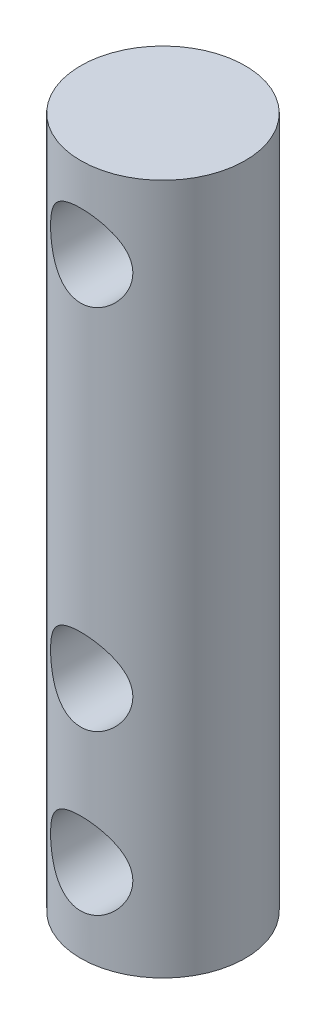
SolidWorks part; units mm, degrees
material "Plain Carbon Steel"
ref_plane "Front Plane" through (0, 0, 0) normal (0, 0, 1) x (1, 0, 0)
ref_plane "Top Plane" through (0, 0, 0) normal (0, 1, 0) x (1, 0, 0)
ref_plane "Right Plane" through (0, 0, 0) normal (1, 0, 0) x (0, 0, -1)
sketch "Sketch1" plane through (0, 0, 0) normal (0, 1, 0) x (1, 0, 0)
  circle A0 centre (0, 0) radius 2.5
  dimension "D1" = 5
extrude "Boss-Extrude1" add sketch "Sketch1" along normal blind 21
sketch "Sketch2" plane through (0, 0, 0) normal (0, 0, 1) x (1, 0, 0)
  line L0 (-2.5, 0) -> (2.5, 0) construction
  line L1 (2.5, 21) -> (-2.5, 21) construction
  circle A0 centre (0, 18.5) radius 1.25
  circle A1 centre (0, 2.5) radius 1.25
  circle A2 centre (0, 7.34) radius 1.25
  dimension "D1" = 2.5
  dimension "D4" = 13.66
  dimension "D2" = 2.5
  dimension "D3" = 2.5
extrude "Cut-Extrude1" cut sketch "Sketch2" against normal through all both and the other way through all
